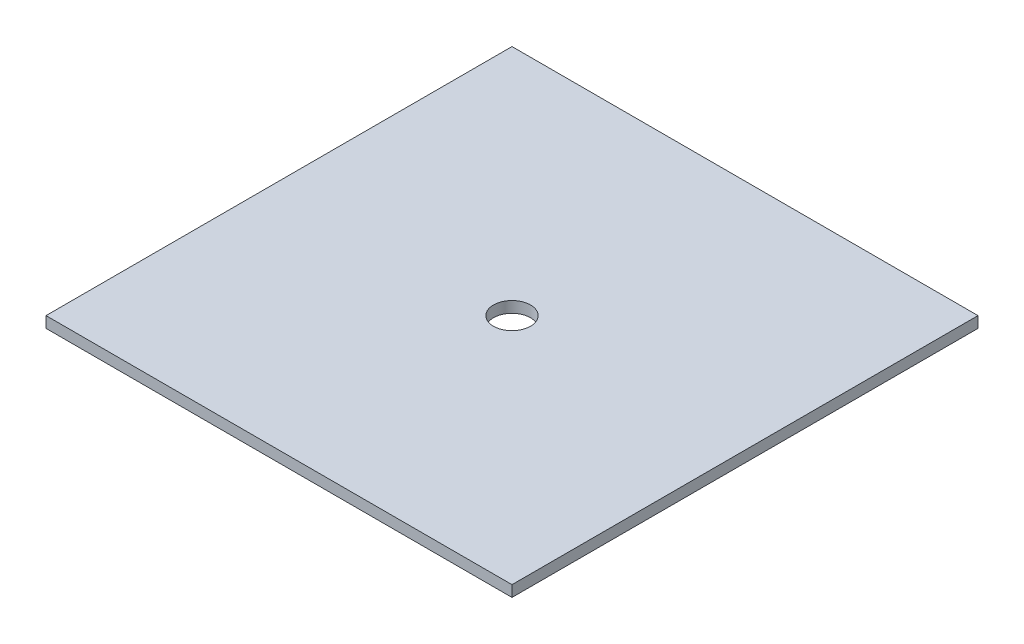
SolidWorks part; units mm, degrees
ref_plane "Front Plane" through (0, 0, 0) normal (0, 0, 1) x (1, 0, 0)
ref_plane "Top Plane" through (0, 0, 0) normal (0, 1, 0) x (1, 0, 0)
ref_plane "Right Plane" through (0, 0, 0) normal (1, 0, 0) x (0, 0, -1)
sketch "Sketch1" plane through (0, 0, 0) normal (0, 1, 0) x (1, 0, 0)
  line L1 (100, 100) -> (-100, 100)
  line L2 (100, 100) -> (100, -100)
  line L3 (100, -100) -> (-100, -100)
  line L4 (-100, 100) -> (-100, -100)
  line L5 (100, 100) -> (-100, -100) construction
  line L6 (100, -100) -> (-100, 100) construction
  circle A0 centre (0, 0) radius 7.9375
  point P0 (0, 0)
  dimension "D2" = 15.875
  dimension "D1" = 200
extrude "Boss-Extrude1" add sketch "Sketch1" along normal blind 4.7625
